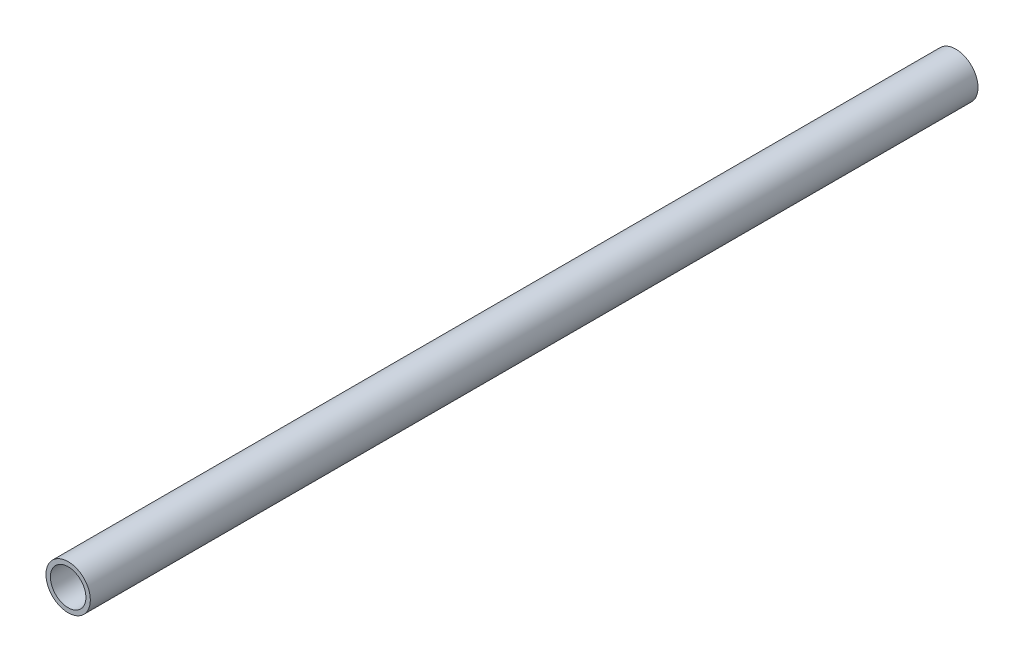
SolidWorks part; units mm, degrees
ref_plane "Front Plane" through (0, 0, 0) normal (0, 0, 1) x (1, 0, 0)
ref_plane "Top Plane" through (0, 0, 0) normal (0, 1, 0) x (1, 0, 0)
ref_plane "Right Plane" through (0, 0, 0) normal (1, 0, 0) x (0, 0, -1)
sketch "Sketch1" plane through (0, 0, 0) normal (0, 0, 1) x (1, 0, 0)
  circle A0 centre (0, 0) radius 5
  circle A1 centre (0, 0) radius 4
extrude "Boss-Extrude1" add sketch "Sketch1" along normal blind 200
